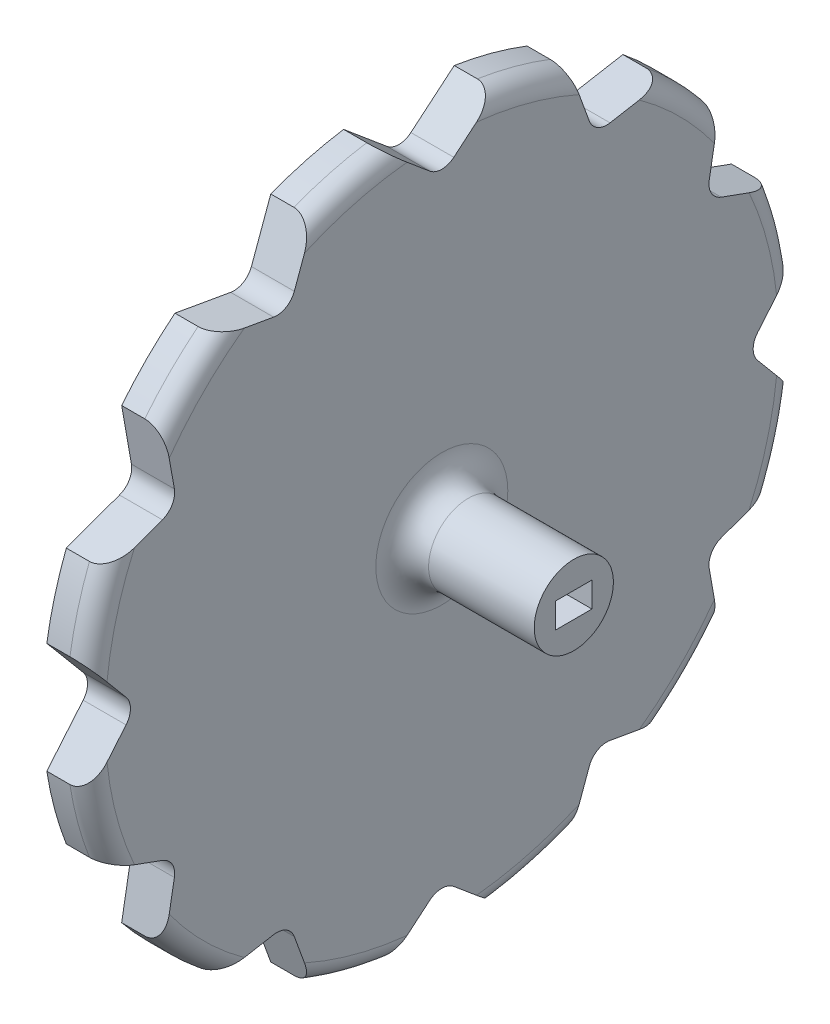
SolidWorks part; units mm, degrees
ref_plane "Спереди" through (0, 0, 0) normal (0, 0, 1) x (1, 0, 0)
ref_plane "Сверху" through (0, 0, 0) normal (0, 1, 0) x (1, 0, 0)
ref_plane "Справа" through (0, 0, 0) normal (1, 0, 0) x (0, 0, -1)
sketch "Sketch1" plane through (0, 0, 0) normal (1, 0, 0) x (0, 0, -1)
  line L0 (1.8159, 47.8359) -> (8.3819, 53.3455)
  line L25 (19.4138, 50.3895) -> (22.3454, 42.3351)
  line L26 (25.4906, 40.5192) -> (33.9317, 42.0076)
  line L27 (42.0076, 33.9317) -> (40.5192, 25.4906)
  line L28 (42.3351, 22.3454) -> (50.3895, 19.4138)
  line L29 (53.3455, 8.3819) -> (47.8359, 1.8159)
  line L30 (47.8359, -1.8159) -> (53.3455, -8.3819)
  line L31 (50.3895, -19.4138) -> (42.3351, -22.3454)
  line L32 (40.5192, -25.4906) -> (42.0076, -33.9317)
  line L33 (33.9317, -42.0076) -> (25.4906, -40.5192)
  line L34 (22.3454, -42.3351) -> (19.4138, -50.3895)
  line L35 (8.3819, -53.3455) -> (1.8159, -47.8359)
  line L36 (-1.8159, -47.8359) -> (-8.3819, -53.3455)
  line L37 (-19.4138, -50.3895) -> (-22.3454, -42.3351)
  line L38 (-25.4906, -40.5192) -> (-33.9317, -42.0076)
  line L39 (-42.0076, -33.9317) -> (-40.5192, -25.4906)
  line L40 (-42.3351, -22.3454) -> (-50.3895, -19.4138)
  line L41 (-53.3455, -8.3819) -> (-47.8359, -1.8159)
  line L42 (-47.8359, 1.8159) -> (-53.3455, 8.3819)
  line L43 (-50.3895, 19.4138) -> (-42.3351, 22.3454)
  line L44 (-40.5192, 25.4906) -> (-42.0076, 33.9317)
  line L45 (-33.9317, 42.0076) -> (-25.4906, 40.5192)
  line L46 (-22.3454, 42.3351) -> (-19.4138, 50.3895)
  line L47 (-8.3819, 53.3455) -> (-1.8159, 47.8359)
  line L48 (0, 0) -> (0, 50) construction
  circle A25 centre (0, 0) radius 50 construction
  arc A26 (-1.8159, 47.8359) -> (1.8159, 47.8359) centre (0, 50) ccw
  arc A27 (22.3454, 42.3351) -> (25.4906, 40.5192) centre (25, 43.3013) ccw
  arc A28 (40.5192, 25.4906) -> (42.3351, 22.3454) centre (43.3013, 25) ccw
  arc A29 (47.8359, 1.8159) -> (47.8359, -1.8159) centre (50, 0) ccw
  arc A30 (42.3351, -22.3454) -> (40.5192, -25.4906) centre (43.3013, -25) ccw
  arc A31 (25.4906, -40.5192) -> (22.3454, -42.3351) centre (25, -43.3013) ccw
  arc A32 (1.8159, -47.8359) -> (-1.8159, -47.8359) centre (0, -50) ccw
  arc A33 (-22.3454, -42.3351) -> (-25.4906, -40.5192) centre (-25, -43.3013) ccw
  arc A34 (-40.5192, -25.4906) -> (-42.3351, -22.3454) centre (-43.3013, -25) ccw
  arc A35 (-47.8359, -1.8159) -> (-47.8359, 1.8159) centre (-50, 0) ccw
  arc A36 (-42.3351, 22.3454) -> (-40.5192, 25.4906) centre (-43.3013, 25) ccw
  arc A37 (-25.4906, 40.5192) -> (-22.3454, 42.3351) centre (-25, 43.3013) ccw
  arc A38 (-50.3895, 19.4138) -> (-53.3455, 8.3819) centre (0, 0) ccw
  arc A39 (-53.3455, -8.3819) -> (-50.3895, -19.4138) centre (0, 0) ccw
  arc A40 (-42.0076, -33.9317) -> (-33.9317, -42.0076) centre (0, 0) ccw
  arc A41 (-19.4138, -50.3895) -> (-8.3819, -53.3455) centre (0, 0) ccw
  arc A42 (8.3819, -53.3455) -> (19.4138, -50.3895) centre (0, 0) ccw
  arc A43 (33.9317, -42.0076) -> (42.0076, -33.9317) centre (0, 0) ccw
  arc A44 (50.3895, -19.4138) -> (53.3455, -8.3819) centre (0, 0) ccw
  arc A45 (53.3455, 8.3819) -> (50.3895, 19.4138) centre (0, 0) ccw
  arc A46 (42.0076, 33.9317) -> (33.9317, 42.0076) centre (0, 0) ccw
  arc A47 (19.4138, 50.3895) -> (8.3819, 53.3455) centre (0, 0) ccw
  arc A48 (-8.3819, 53.3455) -> (-19.4138, 50.3895) centre (0, 0) ccw
  arc A49 (-33.9317, 42.0076) -> (-42.0076, 33.9317) centre (0, 0) ccw
  dimension "D1" = 2.825
  dimension "D2" = 100
  dimension "D5" = 108
  dimension "D4" = 12
  dimension "D3" = 50
extrude "Boss-Extrude1" add sketch "Sketch1" along normal blind 6.5
sketch "Sketch2" plane through (6.5, 0, 0) normal (1, 0, 0) x (0, 0, -1)
  circle A0 centre (0, 0) radius 6
  dimension "D1" = 12
extrude "Boss-Extrude2" add sketch "Sketch2" along normal blind 20
fillet "Fillet1" radius 3 12 edges at (6.5, -13.9762, -52.16) (6.5, -38.1838, -38.1838) (6.5, -52.16, -13.9762) (6.5, -52.16, 13.9762) (6.5, -38.1838, 38.1838) (6.5, -13.9762, 52.16) (6.5, 13.9762, 52.16) (6.5, 38.1838, 38.1838) (6.5, 52.16, 13.9762) (6.5, 52.16, -13.9762) (6.5, 13.9762, -52.16) (6.5, 38.1838, -38.1838)
sketch "Sketch3" plane through (26.5, 0, 0) normal (1, 0, 0) x (0, 0, -1)
  line L1 (-2.75, -1.905) -> (2.75, -1.905)
  line L2 (-2.75, -1.905) -> (-2.75, 1.905)
  line L3 (-2.75, 1.905) -> (2.75, 1.905)
  line L4 (2.75, -1.905) -> (2.75, 1.905)
  line L5 (-2.75, -1.905) -> (2.75, 1.905) construction
  line L6 (-2.75, 1.905) -> (2.75, -1.905) construction
  point P0 (0, 0)
  dimension "D1" = 5.5
  dimension "D2" = 3.81
extrude "Cut-Extrude1" cut sketch "Sketch3" against normal through all
fillet "Fillet2" radius 4 1 edges at (6.5, 0, -6)
